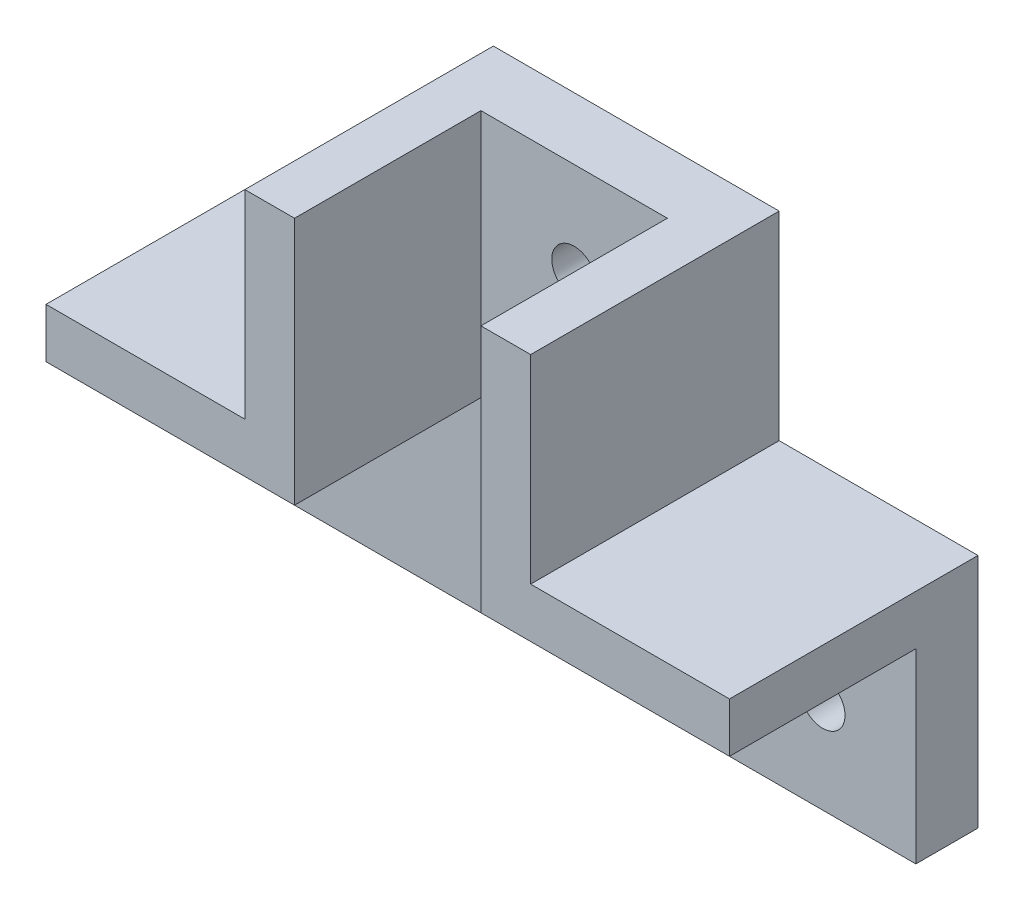
SolidWorks part; units mm, degrees
ref_plane "Front Plane" through (0, 0, 0) normal (0, 0, 1) x (1, 0, 0)
ref_plane "Top Plane" through (0, 0, 0) normal (0, 1, 0) x (1, 0, 0)
ref_plane "Right Plane" through (0, 0, 0) normal (1, 0, 0) x (0, 0, -1)
sketch "Sketch1" plane through (0, 0, 0) normal (0, 0, 1) x (1, 0, 0)
  line L0 (14.3137, -4.2647) -> (34.3137, -4.2647)
  line L1 (-20.6863, -4.2647) -> (-0.6863, -4.2647)
  line L2 (-20.6863, -4.2647) -> (-20.6863, -19.2647)
  line L3 (-20.6863, -19.2647) -> (34.3137, -19.2647)
  line L4 (34.3137, -4.2647) -> (34.3137, -19.2647)
  line L5 (-0.6863, 15.7353) -> (14.3137, 15.7353)
  line L6 (-0.6863, 15.7353) -> (-0.6863, -4.2647)
  line L8 (14.3137, 15.7353) -> (14.3137, -4.2647)
  dimension "D1" = 15
  dimension "D2" = 20
  dimension "D3" = 20
  dimension "D4" = 15
  dimension "D5" = 20
extrude "Boss-Extrude1" add sketch "Sketch1" along normal blind 5
sketch "Sketch2" plane through (0, 0, 0) normal (0, 0, -1) x (-1, 0, 0)
  line L0 (0.6863, 15.7353) -> (4.6863, 15.7353)
  line L1 (4.6863, 15.7353) -> (4.6863, -0.2647)
  line L2 (20.6863, -4.2647) -> (20.6863, -0.2647)
  line L3 (20.6863, -0.2647) -> (6.08, -0.2647)
  line L4 (20.6863, -4.2647) -> (0.6863, -4.2647)
  line L5 (0.6863, 15.7353) -> (0.6863, -4.2647)
  line L6 (6.08, -0.2647) -> (4.6863, -0.2647)
  dimension "D1" = 4
  dimension "D2" = 4
extrude "Boss-Extrude2" add sketch "Sketch2" against normal blind 20 contours L3 L6 L1 L0 L5 L4 L2
sketch "Sketch4" plane through (0, 0, 0) normal (0, 0, -1) x (-1, 0, 0)
  line L0 (20.6863, -19.2647) -> (-34.3137, -19.2647)
  line L1 (-34.3137, -19.2647) -> (-34.3137, -23.2647)
  line L2 (-34.3137, -23.2647) -> (20.6863, -23.2647)
  line L3 (20.6863, -23.2647) -> (20.6863, -19.2647)
  dimension "D1" = 4
ref_plane "Plane4" through (6.8137, 0, 0) normal (-1, 0, 0) x (0, 0, 1)
ref_plane "Plane5" through (-5.6863, 0, 0) normal (-1, 0, 0) x (0, 0, 1)
mirror "Mirror1" about plane through (6.8137, 0, 0) normal (-1, 0, 0) of "Boss-Extrude2"
sketch "Sketch6" plane through (0, 0, 5) normal (0, 0, 1) x (1, 0, 0)
  line L0 (6.8137, 8.8) -> (6.8137, -8.8) construction
  line L1 (-20.6863, -4.2647) -> (-20.6863, -19.2647) construction
  line L2 (-20.6863, -4.2647) -> (-0.6863, -4.2647) construction
  line L3 (34.3137, -4.2647) -> (14.3137, -4.2647) construction
  line L5 (34.3137, -19.2647) -> (34.3137, -4.2647) construction
  line L6 (14.3137, 15.7353) -> (-0.6863, 15.7353) construction
  circle A0 centre (6.8137, 8.2353) radius 1.8
  circle A1 centre (-13.1863, -11.7647) radius 1.8
  circle A2 centre (26.8137, -11.7647) radius 1.8
  dimension "D1" = 3.6
  dimension "D2" = 3.6
  dimension "D3" = 3.6
  dimension "D5" = 7.5
  dimension "D7" = 7.5
  dimension "D8" = 7.5
  dimension "D4" = 7.5
  dimension "D6" = 7.5
ref_plane "Plane6" through (-4.6863, -0.2647, 20) normal (0, -1, 0) x (-1, 0, 0)
extrude "Cut-Extrude3" cut sketch "Sketch6" against normal through all
